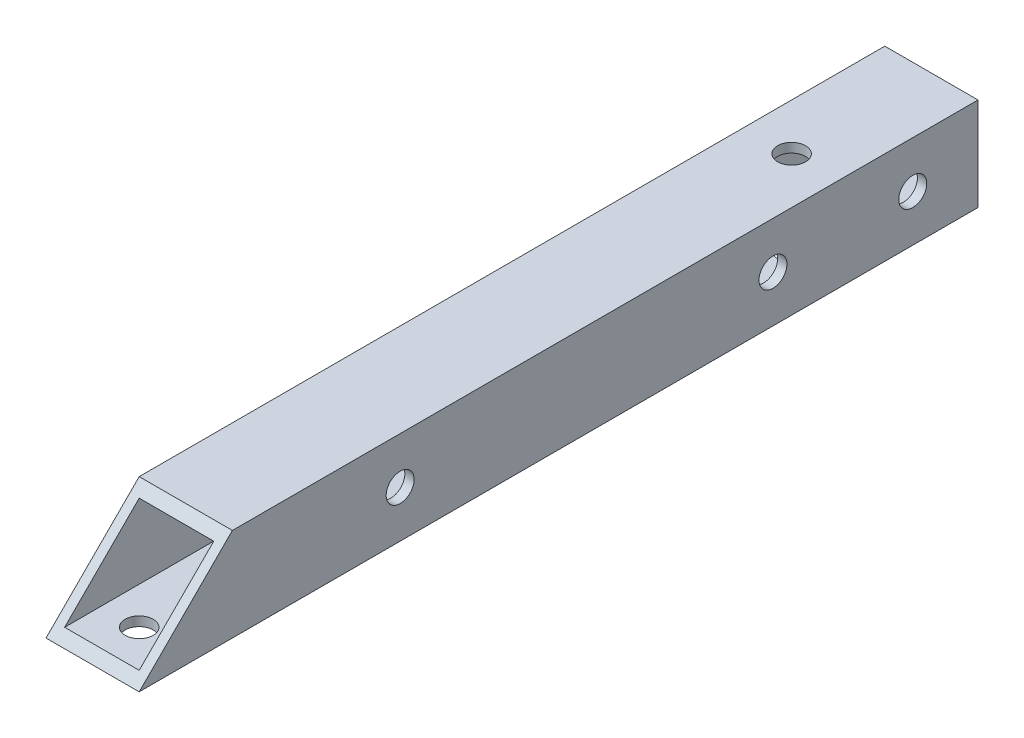
SolidWorks part; units mm, degrees
material "6063-O"
ref_plane "前视基准面" through (0, 0, 0) normal (0, 0, 1) x (1, 0, 0)
ref_plane "上视基准面" through (0, 0, 0) normal (0, 1, 0) x (1, 0, 0)
ref_plane "右视基准面" through (0, 0, 0) normal (1, 0, 0) x (0, 0, -1)
other "Configuration Table"
sketch "草图1" plane through (0, 0, 0) normal (0, 0, 1) x (1, 0, 0)
  line L1 (-5, 5) -> (5, 5)
  line L2 (-5, 5) -> (-5, -5)
  line L3 (-5, -5) -> (5, -5)
  line L4 (5, 5) -> (5, -5)
  line L5 (-5, 5) -> (5, -5) construction
  line L6 (-5, -5) -> (5, 5) construction
  point P4 (0, 0)
  dimension "D1" = 10
  dimension "D2" = 10
extrude "拉伸-薄壁1" add sketch "草图1" along normal blind 90 thin
sketch "草图2" plane through (5, 0, 0) normal (1, 0, 0) x (0, 0, -1)
  line L0 (-90, -5) -> (-90, 5) construction
  line L1 (-90, 0) -> (0, 0) construction
  line L2 (0, -5) -> (0, 5) construction
  circle A0 centre (-62, 0) radius 1.5
  circle A1 centre (-7, 0) radius 1.5
  circle A2 centre (-22, 0) radius 1.5
  dimension "D2" = 3
  dimension "D3" = 15
  dimension "D6" = 40
  dimension "D1" = 7
extrude "切除-拉伸1" cut sketch "草图2" against normal through all
sketch "草图3" plane through (0, 5, 0) normal (0, 1, 0) x (1, 0, 0)
  line L0 (0, 0) -> (0, -90) construction
  line L1 (5, -90) -> (-5, -90) construction
  circle A0 centre (0, -15) radius 1.5
  circle A1 centre (0, -85) radius 1.5
  dimension "D1" = 3
  dimension "D2" = 70
  dimension "D3" = 15
extrude "切除-拉伸3" cut sketch "草图3" against normal through all
sketch "草图4" plane through (-5, 0, 0) normal (-1, 0, 0) x (0, 0, 1)
  line L0 (90, -5) -> (80, 5)
  line L1 (90, -5) -> (0, -5) construction
  line L2 (90, 5) -> (0, 5) construction
  line L3 (80, 5) -> (90, 5)
  line L4 (90, 5) -> (90, -5) construction
  line L5 (90, 5) -> (90, -5)
  dimension "D1" = 45
extrude "切除-拉伸4" cut sketch "草图4" against normal blind 10
